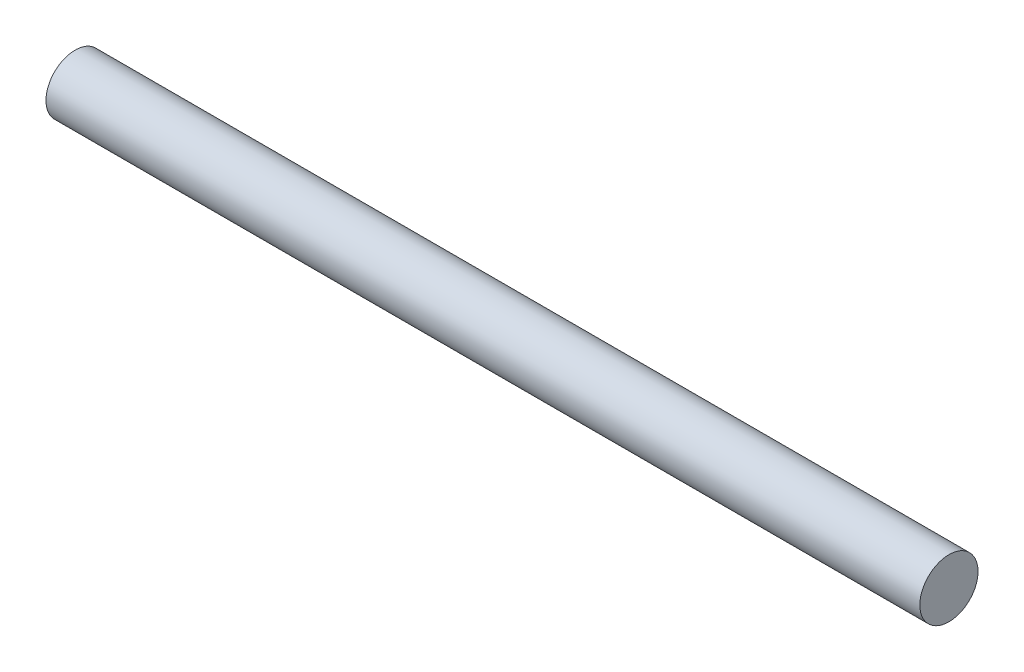
SolidWorks part; units mm, degrees
ref_plane "Front Plane" through (0, 0, 0) normal (0, 0, 1) x (1, 0, 0)
ref_plane "Top Plane" through (0, 0, 0) normal (0, 1, 0) x (1, 0, 0)
ref_plane "Right Plane" through (0, 0, 0) normal (1, 0, 0) x (0, 0, -1)
sketch "Sketch1" plane through (0, 0, 0) normal (0, 1, 0) x (1, 0, 0)
  line L2 (145.4495, 6) -> (145.4495, 12)
  line L3 (145.4495, 12) -> (-34.7205, 12)
  line L4 (-34.7205, 6) -> (-34.7205, 12)
  line L5 (0, 0) -> (-34.7205, 12) construction
  line L6 (145.4495, 12) -> (0, 0) construction
  line L7 (-34.7205, 6) -> (145.4495, 6) construction
  line L8 (-34.7205, 6) -> (145.4495, 6)
  point P0 (0, 0)
  dimension "D1" = 6
  dimension "D2" = 180.17
revolve "Revolve1" add sketch "Sketch1" angle 360 about L8
